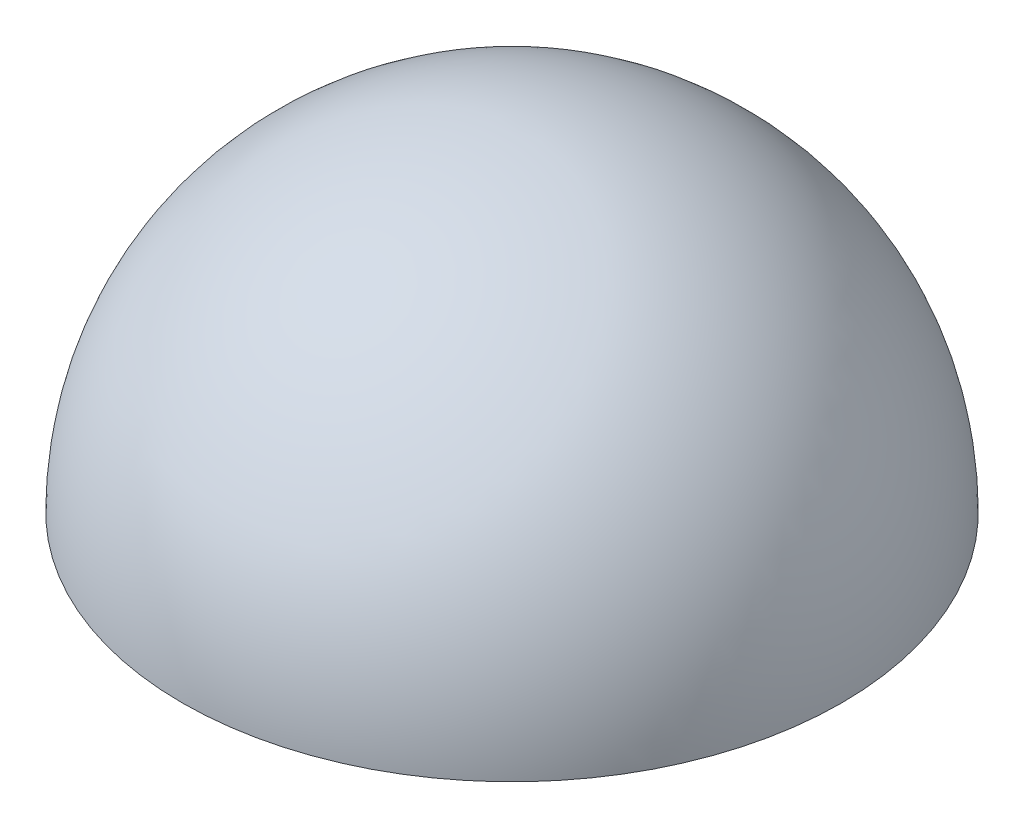
SolidWorks part; units mm, degrees
ref_plane "Front Plane" through (0, 0, 0) normal (0, 0, 1) x (1, 0, 0)
ref_plane "Top Plane" through (0, 0, 0) normal (0, 1, 0) x (1, 0, 0)
ref_plane "Right Plane" through (0, 0, 0) normal (1, 0, 0) x (0, 0, -1)
sketch "Sketch1" plane through (0, 0, 0) normal (0, 0, 1) x (1, 0, 0)
  line L1 (0, 2) -> (3, 2)
  line L2 (0, 2) -> (0, 5)
  arc A0 (0, 5) -> (3, 2) centre (0, 2) cw
  dimension "D2" = 3
revolve "Revolve1" add sketch "Sketch1" angle 360 about L2
